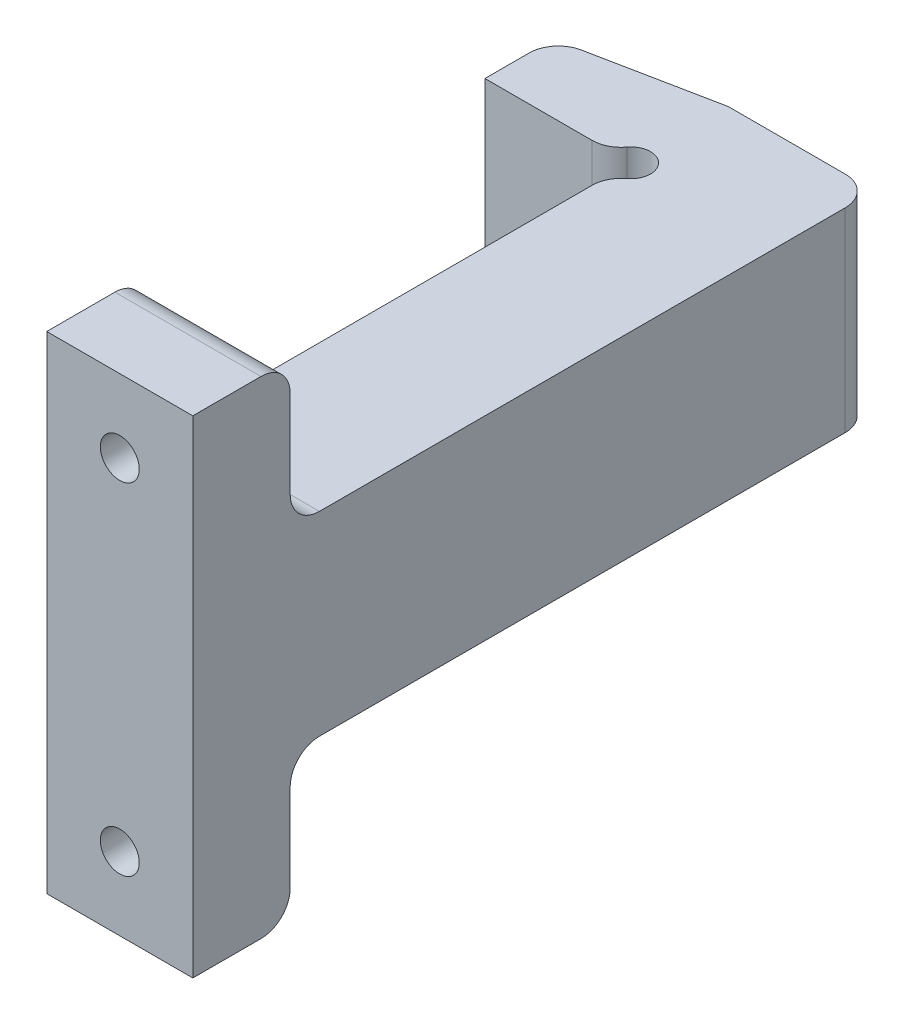
SolidWorks part; units mm, degrees
ref_plane "Front Plane" through (0, 0, 0) normal (0, 0, 1) x (1, 0, 0)
ref_plane "Top Plane" through (0, 0, 0) normal (0, 1, 0) x (1, 0, 0)
ref_plane "Right Plane" through (0, 0, 0) normal (1, 0, 0) x (0, 0, -1)
sketch "Sketch1" plane through (0, 0, 0) normal (0, 1, 0) x (1, 0, 0)
  line L0 (0, 0) -> (-13, 0)
  line L1 (-13, 0) -> (-13, 7)
  line L2 (-13, 7) -> (2, 10)
  line L3 (2, 10) -> (17, 10)
  line L4 (17, 10) -> (17, -60)
  line L5 (17, -60) -> (2, -60)
  line L6 (2, -60) -> (2, -2)
  arc A0 (2, -2) -> (0, 0) centre (2, 0) ccw
  dimension "D5" = 2
  dimension "D1" = 15
  dimension "D2" = 7
  dimension "D3" = 10
  dimension "D4" = 15
  dimension "D6" = 60
  dimension "D7" = 15
extrude "Boss-Extrude1" add sketch "Sketch1" along normal blind 20
sketch "Sketch2" plane through (0, 0, 60) normal (0, 0, 1) x (1, 0, 0)
  line L0 (9.5, 27.5) -> (2, 27.5) construction
  line L1 (2, 20) -> (17, 20)
  line L2 (2, 20) -> (2, 35)
  line L3 (2, 35) -> (17, 35)
  line L4 (17, 20) -> (17, 35)
  line L5 (9.5, 27.5) -> (9.5, 20) construction
  line L6 (17, 20) -> (17, 0) construction
  line L7 (2, 10) -> (17, 10) construction
  line L8 (2, 20) -> (2, 0) construction
  line L9 (9.5, -7.5) -> (9.5, 0) construction
  line L10 (9.5, -7.5) -> (2, -7.5) construction
  line L11 (17, 0) -> (17, -15)
  line L12 (2, -15) -> (17, -15)
  line L13 (2, 0) -> (2, -15)
  line L14 (2, 0) -> (17, 0)
  circle A0 centre (9.5, 27.5) radius 2
  circle A1 centre (9.5, -7.5) radius 2
  dimension "D1" = 4
  dimension "D2" = 15
extrude "Boss-Extrude2" add sketch "Sketch2" against normal blind 10
fillet "Fillet1" radius 3 9 edges at (0, 10, 0) (2, 10, 2) (9.5, -15, 50) (9.5, 0, 50) (-13, 10, -7) (2, 10, -10) (17, 10, -10) (9.5, 20, 50) (9.5, 35, 50)
